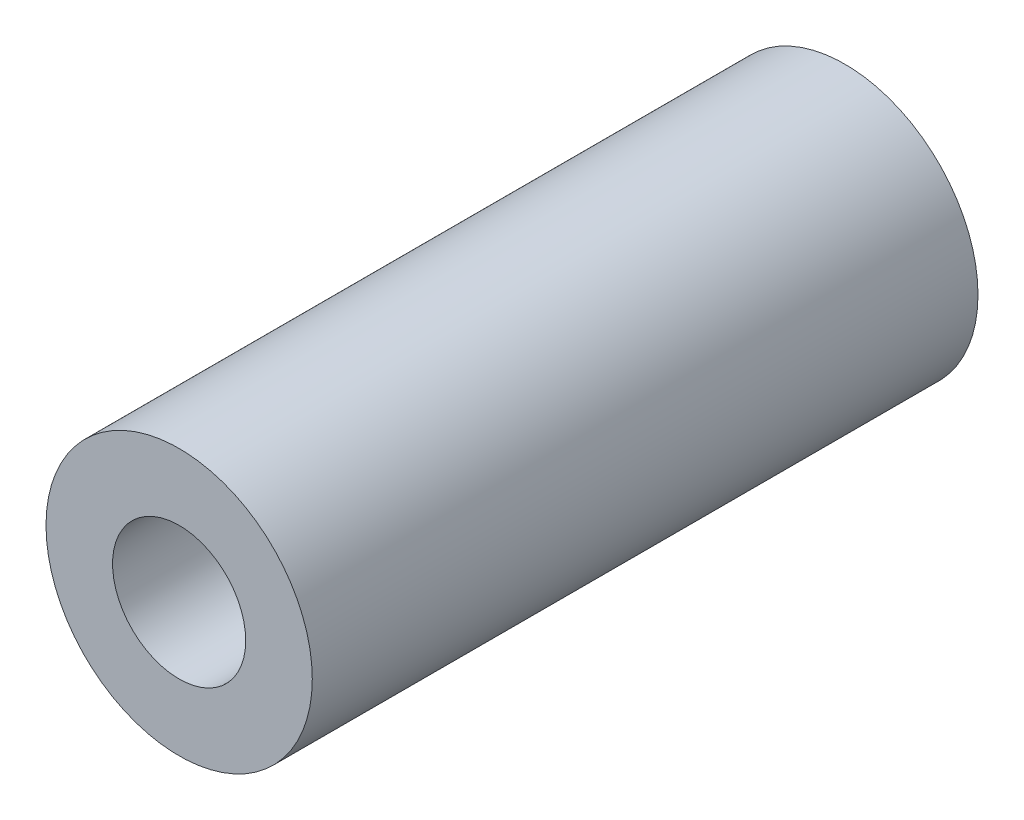
SolidWorks part; units mm, degrees
ref_plane "Front Plane" through (0, 0, 0) normal (0, 0, 1) x (1, 0, 0)
ref_plane "Top Plane" through (0, 0, 0) normal (0, 1, 0) x (1, 0, 0)
ref_plane "Right Plane" through (0, 0, 0) normal (1, 0, 0) x (0, 0, -1)
sketch "Sketch1" plane through (0, 0, 0) normal (0, 0, 1) x (1, 0, 0)
  circle A0 centre (0, 0) radius 2
  dimension "D1" = 4
extrude "Extrude-Thin1" add sketch "Sketch1" along normal blind 10 thin thin type one direction reverse wall 1
